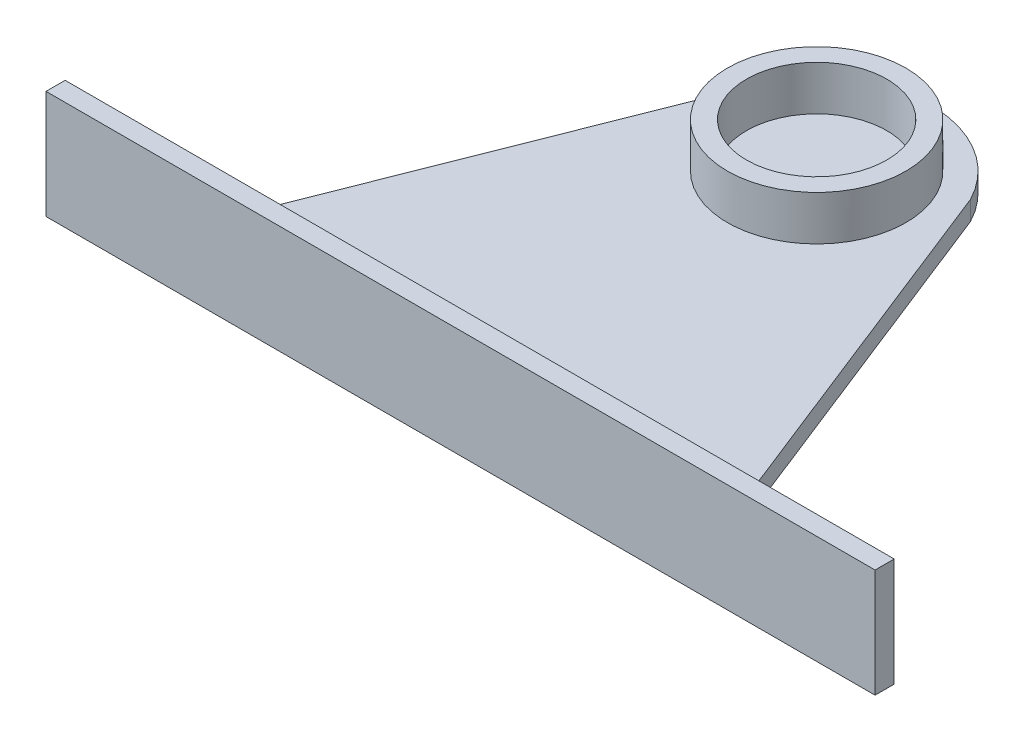
SolidWorks part; units mm, degrees
ref_plane "Front Plane" through (0, 0, 0) normal (0, 0, 1) x (1, 0, 0)
ref_plane "Top Plane" through (0, 0, 0) normal (0, 1, 0) x (1, 0, 0)
ref_plane "Right Plane" through (0, 0, 0) normal (1, 0, 0) x (0, 0, -1)
sketch "Sketch1" plane through (0, 0, 0) normal (0, 1, 0) x (1, 0, 0)
  line L0 (-48.9291, -17.8351) -> (31.0709, -17.8351)
  line L1 (31.0709, -17.8351) -> (6.9855, 43.197)
  line L2 (-24.8438, 43.197) -> (-48.9291, -17.8351)
  line L3 (-8.9291, -17.8351) -> (-8.9291, 35.0049) construction
  arc A0 (-24.8438, 43.197) -> (6.9855, 43.197) centre (-8.9291, 35.0049) cw
  circle A1 centre (-8.9291, 35.0049) radius 11 construction
  dimension "D3" = 22
  dimension "D1" = 80
  dimension "D4" = 52.84
extrude "Boss-Extrude1" add sketch "Sketch1" along normal blind 3
sketch "Sketch2" plane through (0, 3, 0) normal (0, 1, 0) x (1, 0, 0)
  circle A0 centre (-8.9291, 35.0049) radius 11
  circle A1 centre (-8.9291, 35.0049) radius 14
  dimension "D1" = 28
  dimension "D2" = 22
extrude "Boss-Extrude2" add sketch "Sketch2" along normal blind 7
sketch "Sketch3" plane through (0, 0, 17.8351) normal (0, 0, 1) x (1, 0, 0)
  line L0 (31.0709, 3) -> (31.0709, 0) construction
  line L1 (-73.9291, -7.7495) -> (56.0709, -7.7495)
  line L2 (-73.9291, -7.7495) -> (-73.9291, 9.2505)
  line L3 (-73.9291, 9.2505) -> (56.0709, 9.2505)
  line L4 (56.0709, -7.7495) -> (56.0709, 9.2505)
  line L6 (-48.9291, 3) -> (-48.9291, 0) construction
  dimension "D1" = 25
  dimension "D2" = 17
  dimension "D3" = 130
  dimension "D4" = 25
extrude "Boss-Extrude3" add sketch "Sketch3" along normal blind 3
sketch "Sketch4" plane through (0, 0, 17.8351) normal (0, 0, -1) x (-1, 0, 0)
  line L0 (-56.0709, 9.2505) -> (73.9291, 9.2505) construction
  circle A0 centre (-23.299, 5.7505) radius 2.5726
  dimension "D2" = 5.1453
  dimension "D1" = 3.5
